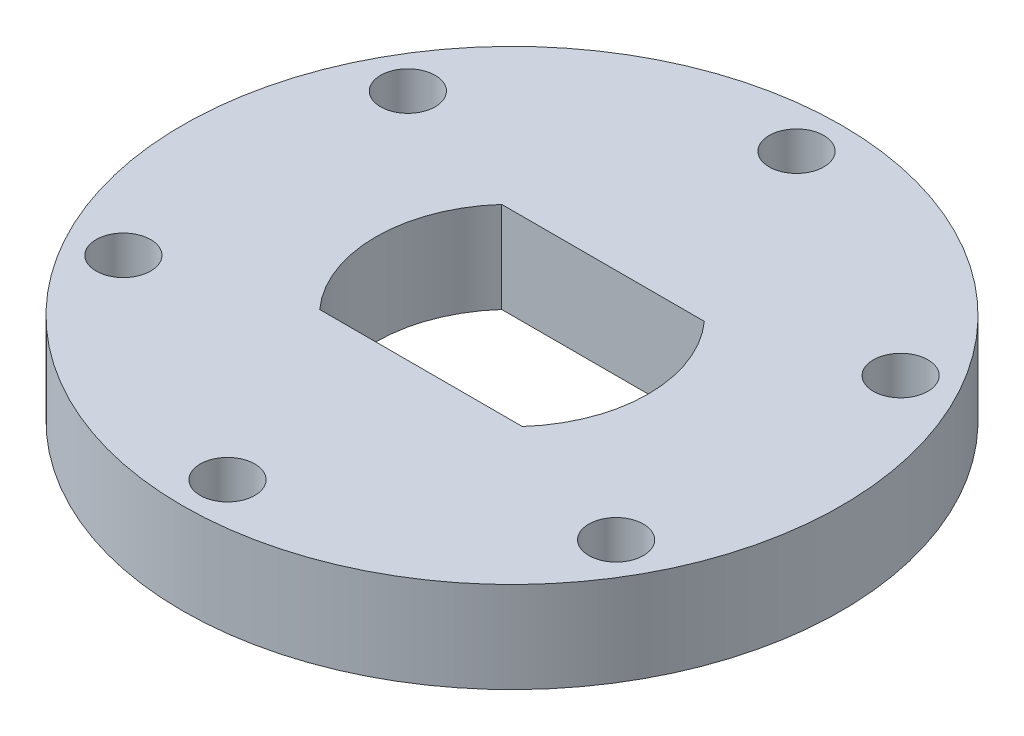
SolidWorks part; units mm, degrees
material "6061-T6 (SS)"
ref_plane "Front Plane" through (0, 0, 0) normal (0, 0, 1) x (1, 0, 0)
ref_plane "Top Plane" through (0, 0, 0) normal (0, 1, 0) x (1, 0, 0)
ref_plane "Right Plane" through (0, 0, 0) normal (1, 0, 0) x (0, 0, -1)
sketch "Sketch1" plane through (0, 0, 0) normal (0, 1, 0) x (1, 0, 0)
  line L0 (0, 0) -> (0, 19.8438) construction
  line L1 (-7.0659, -6.35) -> (7.0659, -6.35)
  line L3 (-7.0659, 6.35) -> (7.0659, 6.35)
  line L7 (0, 0) -> (17.1852, 9.9219) construction
  line L8 (17.1852, -9.9219) -> (0, 0) construction
  line L9 (0, 0) -> (0, -19.8437) construction
  line L10 (-17.1852, -9.9219) -> (0, 0) construction
  line L11 (0, 0) -> (-17.1852, 9.9219) construction
  circle A0 centre (0, 0) radius 22.987
  arc A1 (-7.0659, 6.35) -> (-7.0659, -6.35) centre (0, 0) ccw
  arc A2 (7.0659, -6.35) -> (7.0659, 6.35) centre (0, 0) ccw
  circle A3 centre (0, 19.8438) radius 1.905
  circle A4 centre (17.1852, 9.9219) radius 1.905
  circle A5 centre (17.1852, -9.9219) radius 1.905
  circle A6 centre (0, -19.8437) radius 1.905
  circle A7 centre (-17.1852, -9.9219) radius 1.905
  circle A8 centre (-17.1852, 9.9219) radius 1.905
  point P26 (0, 0)
  dimension "D1" = 45.974
  dimension "D2" = 19
  dimension "D4" = 3.81
  dimension "D3" = 12.7
  dimension "D5" = 19.8438
  dimension "D6" = 6.35
  dimension "D7" = 6
extrude "Boss-Extrude1" add sketch "Sketch1" along normal blind 6.35
